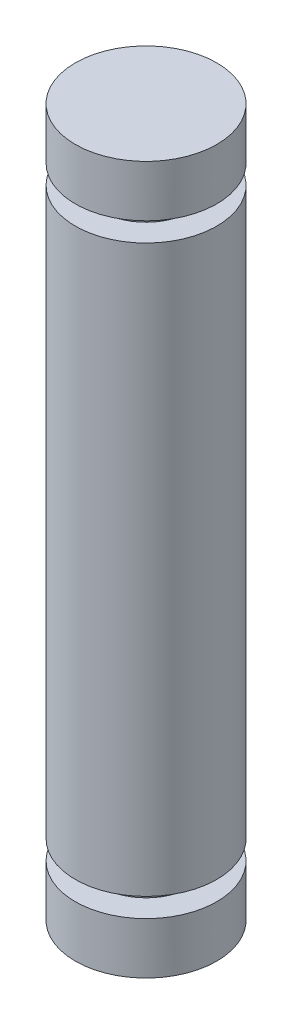
SolidWorks part; units mm, degrees
ref_plane "Front Plane" through (0, 0, 0) normal (0, 0, 1) x (1, 0, 0)
ref_plane "Top Plane" through (0, 0, 0) normal (0, 1, 0) x (1, 0, 0)
ref_plane "Right Plane" through (0, 0, 0) normal (1, 0, 0) x (0, 0, -1)
sketch "Sketch2" plane through (0, 0, 0) normal (0, 1, 0) x (1, 0, 0)
  circle A0 centre (0, 0) radius 2.5
  dimension "D1" = 5
extrude "Boss-Extrude1" add sketch "Sketch2" along normal blind 25
sketch "Sketch3" plane through (0, 0, 0) normal (1, 0, 0) x (0, 0, -1)
  line L0 (-2.5, 0) -> (-2.5, 1.82) construction
  line L1 (-2.5, 25) -> (-2.5, 0) construction
  line L2 (-2.5, 1.82) -> (-1.6, 1.82)
  line L3 (-1.6, 1.82) -> (-1.6, 2.5)
  line L4 (-1.6, 2.5) -> (-2.5, 2.5)
  line L5 (-2.5, 2.5) -> (-2.5, 1.82)
  line L6 (2.5, 0) -> (2.5, 1.82) construction
  line L7 (2.5, 0) -> (2.5, 25) construction
  line L8 (2.5, 1.82) -> (1.6, 1.82) construction
  line L9 (1.6, 1.82) -> (1.6, 2.5) construction
  line L10 (1.6, 2.5) -> (2.5, 2.5) construction
  line L11 (2.5, 2.5) -> (2.5, 1.82) construction
  line L12 (0, 0) -> (0, 25) construction
  line L13 (2.5, 25) -> (-2.5, 25) construction
  line L14 (-2.5, 12.5) -> (2.5, 12.5) construction
  line L15 (-2.5, 25) -> (-2.5, 23.18) construction
  line L16 (-2.5, 22.5) -> (-2.5, 23.18)
  line L17 (-1.6, 22.5) -> (-2.5, 22.5)
  line L18 (-1.6, 23.18) -> (-1.6, 22.5)
  line L19 (-2.5, 23.18) -> (-1.6, 23.18)
  point P23 (-1.6, 1.8228)
  dimension "D1" = 2.5
  dimension "D2" = 3.2
  dimension "D3" = 0.68
revolve "Cut-Revolve1" cut sketch "Sketch3" angle 360 about L12
